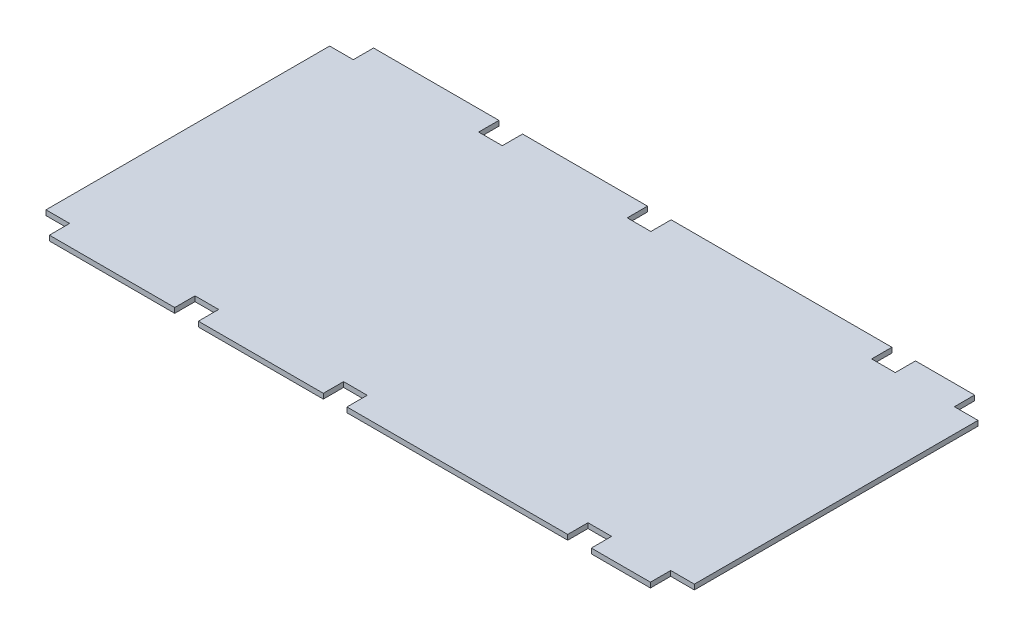
SolidWorks part; units mm, degrees
ref_plane "Front Plane" through (0, 0, 0) normal (0, 0, 1) x (1, 0, 0)
ref_plane "Top Plane" through (0, 0, 0) normal (0, 1, 0) x (1, 0, 0)
ref_plane "Right Plane" through (0, 0, 0) normal (1, 0, 0) x (0, 0, -1)
sketch "Sketch1" plane through (0, 0, 0) normal (0, 1, 0) x (1, 0, 0)
  line L1 (0, 1219.2) -> (2438.4, 1219.2)
  line L2 (0, 1219.2) -> (0, 0)
  line L3 (0, 0) -> (2438.4, 0)
  line L4 (2438.4, 1219.2) -> (2438.4, 0)
  dimension "D1" = 1219.2
  dimension "D2" = 2438.4
extrude "Boss-Extrude1" add sketch "Sketch1" along normal mid plane 19.05
sketch "Sketch2" plane through (0, 9.525, 0) normal (0, 1, 0) x (1, 0, 0)
  line L5 (2438.4, 1219.2) -> (0, 1219.2) construction
  line L7 (0, 1219.2) -> (88.9, 1219.2)
  line L8 (0, 1219.2) -> (0, 1143)
  line L9 (0, 1143) -> (88.9, 1143)
  line L10 (88.9, 1219.2) -> (88.9, 1143)
  line L11 (560.3875, 1219.2) -> (649.2875, 1219.2)
  line L12 (560.3875, 1219.2) -> (560.3875, 1143)
  line L13 (560.3875, 1143) -> (649.2875, 1143)
  line L15 (2438.4, 0) -> (2438.4, 1219.2) construction
  line L18 (1119.1875, 1143) -> (1208.0875, 1143)
  line L19 (1208.0875, 1219.2) -> (1208.0875, 1143)
  line L20 (2038.35, 1219.2) -> (2127.25, 1219.2)
  line L21 (2038.35, 1219.2) -> (2038.35, 1143)
  line L22 (2038.35, 1143) -> (2127.25, 1143)
  line L23 (2127.25, 1219.2) -> (2127.25, 1143)
  line L24 (2349.5, 1219.2) -> (2438.4, 1219.2)
  line L25 (2349.5, 1219.2) -> (2349.5, 1143)
  line L26 (2349.5, 1143) -> (2438.4, 1143)
  line L27 (2438.4, 1219.2) -> (2438.4, 1143)
  line L28 (649.2875, 1219.2) -> (649.2875, 1143)
  line L29 (0, 1219.2) -> (0, 0) construction
  line L30 (1208.0875, 1219.2) -> (1119.1875, 1219.2)
  line L31 (1119.1875, 1219.2) -> (1119.1875, 1143)
  line L32 (0, 609.6) -> (2438.4, 609.6) construction
  line L33 (1119.1875, 0) -> (1119.1875, 76.2)
  line L34 (1208.0875, 0) -> (1119.1875, 0)
  line L35 (649.2875, 0) -> (649.2875, 76.2)
  line L36 (2438.4, 0) -> (2438.4, 76.2)
  line L37 (2349.5, 76.2) -> (2438.4, 76.2)
  line L38 (2349.5, 0) -> (2349.5, 76.2)
  line L39 (2349.5, 0) -> (2438.4, 0)
  line L40 (2127.25, 0) -> (2127.25, 76.2)
  line L41 (2038.35, 76.2) -> (2127.25, 76.2)
  line L42 (2038.35, 0) -> (2038.35, 76.2)
  line L43 (2038.35, 0) -> (2127.25, 0)
  line L44 (1208.0875, 0) -> (1208.0875, 76.2)
  line L45 (1119.1875, 76.2) -> (1208.0875, 76.2)
  line L46 (560.3875, 76.2) -> (649.2875, 76.2)
  line L47 (560.3875, 0) -> (560.3875, 76.2)
  line L48 (560.3875, 0) -> (649.2875, 0)
  line L49 (88.9, 0) -> (88.9, 76.2)
  line L50 (0, 76.2) -> (88.9, 76.2)
  line L51 (0, 0) -> (0, 76.2)
  line L52 (0, 0) -> (88.9, 0)
  point P25 (0, 1181.1)
  point P27 (1208.0875, 1181.1)
  dimension "D1" = 76.2
  dimension "D2" = 88.9
  dimension "D3" = 560.3875
  dimension "D4" = 649.2875
  dimension "D5" = 88.9
  dimension "D6" = 311.15
  dimension "D7" = 400.05
  dimension "D8" = 830.2625
  dimension "D9" = 88.9
extrude "Cut-Extrude1" cut sketch "Sketch2" against normal through all
